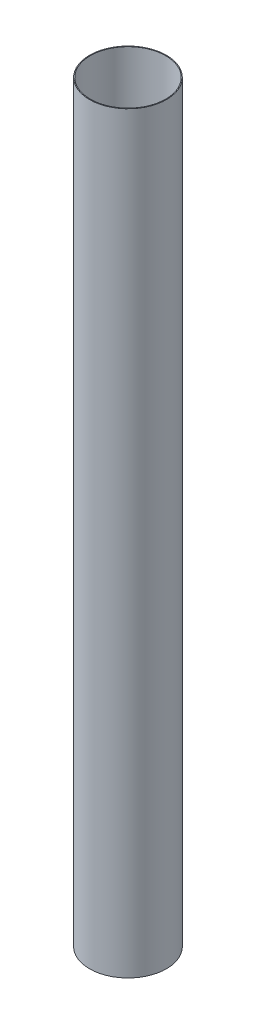
SolidWorks part; units mm, degrees
material "Hexcel AS4C (3000 Filaments)"
ref_plane "Front Plane" through (0, 0, 0) normal (0, 0, 1) x (1, 0, 0)
ref_plane "Top Plane" through (0, 0, 0) normal (0, 1, 0) x (1, 0, 0)
ref_plane "Right Plane" through (0, 0, 0) normal (1, 0, 0) x (0, 0, -1)
sketch "Sketch1" plane through (0, 0, 0) normal (0, 1, 0) x (1, 0, 0)
  circle A0 centre (0, 0) radius 76.2889
  circle A1 centre (0, 0) radius 77.8637
  dimension "D1" = 152.5778
  dimension "D2" = 155.7274
extrude "Boss-Extrude1" add sketch "Sketch1" along normal blind 1524
